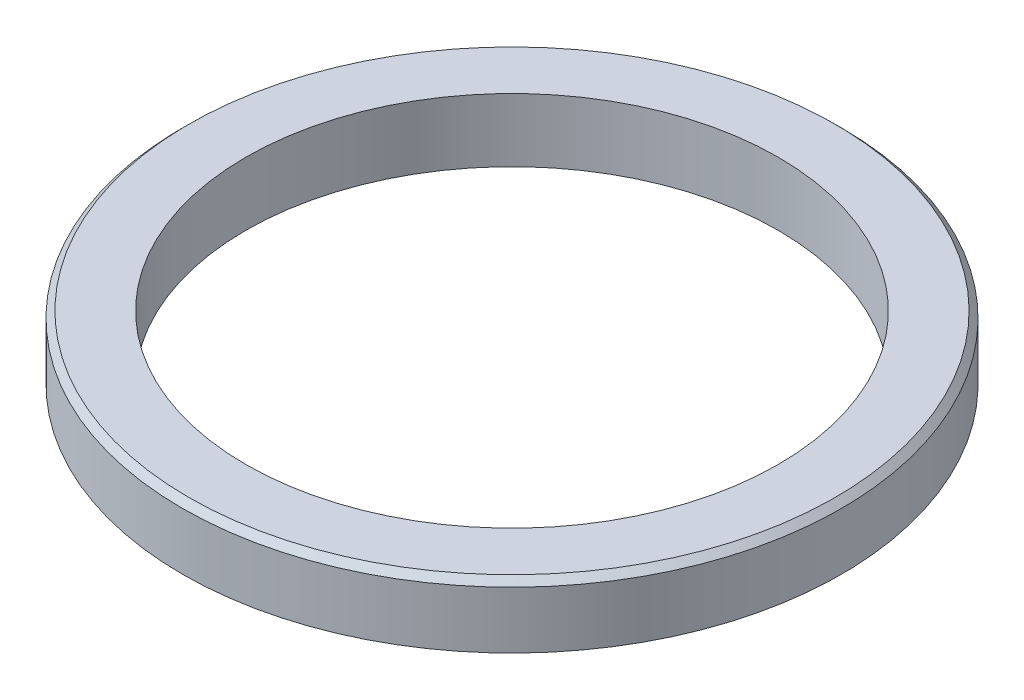
SolidWorks part; units mm, degrees
ref_plane "前视基准面" through (0, 0, 0) normal (0, 0, 1) x (1, 0, 0)
ref_plane "上视基准面" through (0, 0, 0) normal (0, 1, 0) x (1, 0, 0)
ref_plane "右视基准面" through (0, 0, 0) normal (1, 0, 0) x (0, 0, -1)
sketch "草图1" plane through (0, 0, 0) normal (0, 1, 0) x (1, 0, 0)
  circle A0 centre (0, 0) radius 26
  dimension "D1" = 52
extrude "凸台-拉伸1" add sketch "草图1" along normal blind 5
chamfer "倒角1" distance 0.5 angle 45 1 edges at (0, 5, 26)
sketch "草图2" plane through (0, 5, 0) normal (0, 1, 0) x (1, 0, 0)
  circle A0 centre (0, 0) radius 21
  dimension "D1" = 42
extrude "切除-拉伸1" cut sketch "草图2" against normal blind 10
